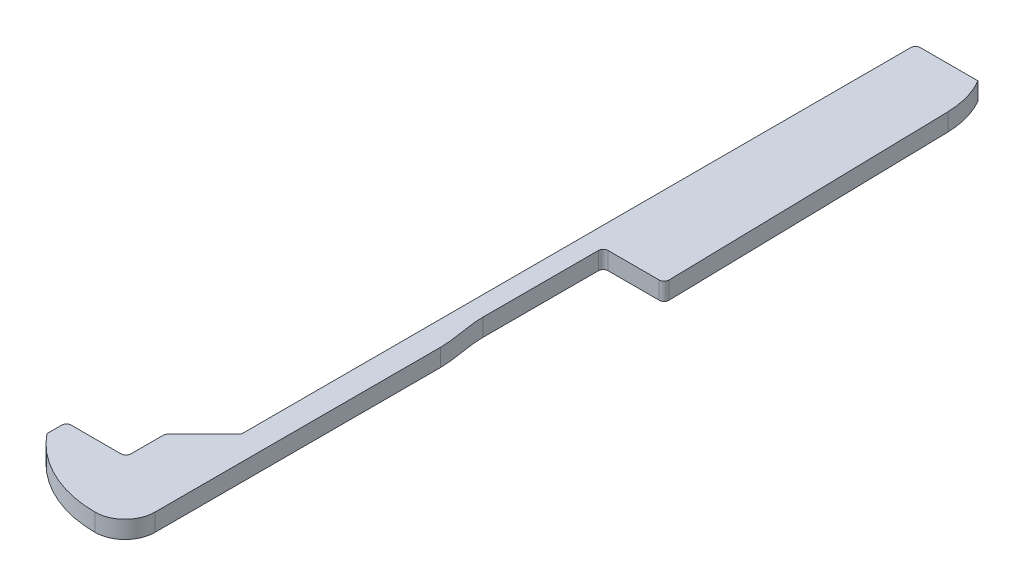
SolidWorks part; units mm, degrees
ref_plane "Front Plane" through (0, 0, 0) normal (0, 0, 1) x (1, 0, 0)
ref_plane "Top Plane" through (0, 0, 0) normal (0, 1, 0) x (1, 0, 0)
ref_plane "Right Plane" through (0, 0, 0) normal (1, 0, 0) x (0, 0, -1)
sketch "Sketch1" plane through (0, 0, 0) normal (0, 1, 0) x (1, 0, 0)
  line L0 (0, 4.5) -> (0, 6.5)
  line L1 (0, 0) -> (18.25, 0) construction
  line L2 (0, 0) -> (0, 83.5) construction
  line L3 (0, 83.5) -> (18.25, 83.5) construction
  line L4 (18.25, 0) -> (18.25, 83.5) construction
  line L5 (0, 6.5) -> (6.1, 6.5)
  line L6 (6.1, 6.5) -> (6.1, 10.5)
  line L7 (6.1, 10.5) -> (10, 14.4)
  line L8 (10, 14.4) -> (10, 83.5)
  line L9 (17.602, 79.1992) -> (18.25, 49.5)
  line L10 (18.25, 49.5) -> (12, 49.5)
  line L11 (12, 37.18) -> (12, 49.5)
  line L12 (12.5, 32.33) -> (12.5, 3.07)
  line L13 (10, 83.5) -> (16.4, 83.5)
  line L14 (12, 39.12) -> (12, 35.2194) construction
  line L15 (12.5, 33.6165) -> (12.5, 30.9888) construction
  arc A0 (17.602, 79.1992) -> (16.4, 83.5) centre (8.6041, 79.0029) ccw
  arc A1 (12.5, 3.07) -> (9.43, 0) centre (9.43, 3.07) cw
  arc A2 (9.43, 0) -> (0, 4.5) centre (9.43, 12.1305) cw
  spline S0 degree 3 poles (12.5, 32.33) (12.5, 33.9723) (12, 35.5548) (12, 37.18) knots 0 0 0 0 1 1 1 1
  point P5 (16.4, 83.5)
  point P6 (0, 4.5)
  point P7 (0, 6.5)
  point P8 (18.25, 49.5)
  dimension "D11" = 3.9
  dimension "D12" = 9
  dimension "D1" = 83.5
  dimension "D2" = 18.25
  dimension "D3" = 1.85
  dimension "D4" = 34
  dimension "D5" = 4.5
  dimension "D6" = 2
  dimension "D7" = 6.1
  dimension "D8" = 4
  dimension "D9" = 45
  dimension "D10" = 1.25
  dimension "D13" = 6.25
  dimension "D14" = 12.32
  dimension "D15" = 4.85
  dimension "D16" = 29.26
  dimension "D17" = 2.5
extrude "Boss-Extrude1" add sketch "Sketch1" along normal blind 1.8
fillet "Fillet2" radius 0.5 7 edges at (12, 0.9, -49.5) (18.25, 0.9, -49.5) (10, 0.9, -14.4) (6.1, 0.9, -10.5) (6.1, 0.9, -6.5) (10, 0.9, -83.5) (0, 0.9, -6.5)
